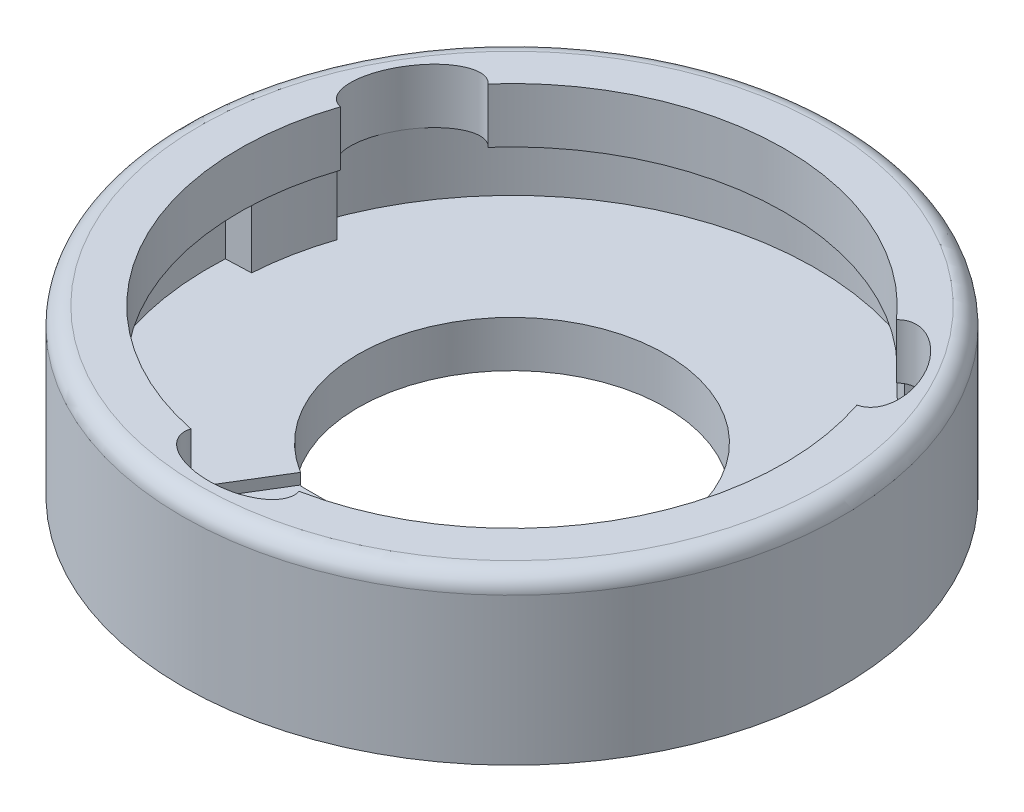
SolidWorks part; units mm, degrees
ref_plane "Ebene vorne" through (0, 0, 0) normal (0, 0, 1) x (1, 0, 0)
ref_plane "Ebene oben" through (0, 0, 0) normal (0, 1, 0) x (1, 0, 0)
ref_plane "Ebene rechts" through (0, 0, 0) normal (1, 0, 0) x (0, 0, -1)
sketch "Skizze1" plane through (0, 0, 0) normal (0, 1, 0) x (1, 0, 0)
  circle A0 centre (0, 0) radius 7.5
  circle A3 centre (0, 0) radius 3.5
extrude "Aufsatz-Linear austragen2" add sketch "Skizze1" along normal blind 0.8
sketch "Skizze5" plane through (0, 0.8, 0) normal (0, 1, 0) x (1, 0, 0)
  circle A0 centre (0, 0) radius 6.9
  circle A1 centre (0, 0) radius 7.5
extrude "Aufsatz-Linear austragen4" add sketch "Skizze5" along normal blind 1.7
sketch "Skizze18" plane through (0, 2.5, 0) normal (0, 1, 0) x (1, 0, 0)
  circle A0 centre (0, 0) radius 7.5
  circle A1 centre (0, 0) radius 6.2
extrude "Aufsatz-Linear austragen5" add sketch "Skizze18" along normal blind 1.25
sketch "Skizze19" plane through (0, 3.75, 0) normal (0, 1, 0) x (1, 0, 0)
  ellipse E1 centre (0, -6.2) end of major axis (-1.25, -6.2) minor radius 0.7
extrude "Schnitt-Linear austragen1" cut sketch "Skizze19" against normal blind 1.75
sketch "Skizze21" plane through (0, 0.8, 0) normal (0, 1, 0) x (1, 0, 0)
  line L5 (1.25, -6.2) -> (1.5834, -7.331)
  line L6 (2.8203, -5.6611) -> (3.4483, -6.6603)
  arc A9 (1.5834, -7.331) -> (3.4483, -6.6603) centre (0, 0) ccw
  circle A10 centre (0, 0) radius 7.5 construction
  arc A11 (1.25, -6.2) -> (2.8203, -5.6611) centre (0, 0) ccw
  ellipse E0 centre (0, -6.2) end of major axis (-1.25, -6.2) minor radius 0.7 (-1.2304, -6.0767) -> (1.2304, -6.0767) ccw construction
extrude "Aufsatz-Linear austragen6" add sketch "Skizze21" along normal blind 1.7
sketch "Skizze22" plane through (0, 0.8, 0) normal (0, 1, 0) x (1, 0, 0)
  line L2 (1.8267, -2.9855) -> (3.6013, -5.8857)
  line L3 (-1.8267, -2.9855) -> (-3.6013, -5.8857)
  arc A0 (-3.6013, -5.8857) -> (3.6013, -5.8857) centre (0, 0) cw
  arc A1 (3.1278, -6.1503) -> (1.4132, -6.7537) centre (0, 0) ccw construction
  arc A2 (-1.8267, -2.9855) -> (1.8267, -2.9855) centre (0, 0) cw
  circle A3 centre (0, 0) radius 3.5 construction
  arc A4 (3.1278, -6.1503) -> (1.4132, -6.7537) centre (0, 0) ccw construction
  point P1 (-1.5414, -3.1423)
  point P2 (1.5414, -3.1423)
  point P16 (2.084, -2.812)
  point P17 (-1.8267, -2.9855)
  point P18 (1.8267, -2.9855)
extrude "Aufsatz-Linear austragen7" add sketch "Skizze22" along normal blind 0.25
pattern_circular "Kreismuster2" count 3 over 360 about axis through (0, 3.75, 0) along (0, -1, 0) of "Schnitt-Linear austragen1"
pattern_circular "Kreismuster4" count 3 over 360 about axis through (0, 0, 0) along (0, 1, 0) of "Aufsatz-Linear austragen6"
fillet "Verrundung1" radius 0.4 1 edges at (0, 3.75, 7.5)
sketch "Skizze25" plane through (0, 0, 0) normal (0, -1, 0) x (1, 0, 0)
  line L1 (-1.7959, 3.0041) -> (1.8123, 3.0041)
  line L2 (-1.7959, 3.0041) -> (-1.7959, 5.1332)
  line L3 (-1.7959, 5.1332) -> (1.8123, 5.1332)
  line L4 (1.8123, 3.0041) -> (1.8123, 5.1332)
  circle A0 centre (0, 0) radius 3.5 construction
  point P6 (-1.7959, 3.0041)
extrude "Aufsatz-Linear austragen8" add sketch "Skizze25" against normal blind 0.8
